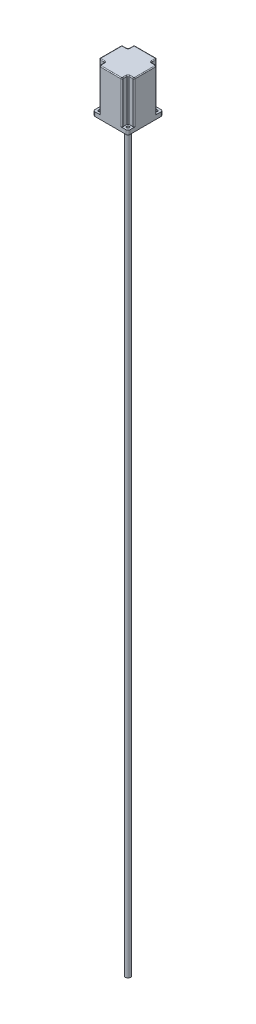
SolidWorks part; units mm, degrees
ref_plane "Спереди" through (0, 0, 0) normal (0, 0, 1) x (1, 0, 0)
ref_plane "Сверху" through (0, 0, 0) normal (0, 1, 0) x (1, 0, 0)
ref_plane "Справа" through (0, 0, 0) normal (1, 0, 0) x (0, 0, -1)
sketch "Эскиз1" plane through (0, 0, 0) normal (0, 1, 0) x (1, 0, 0)
  line L1 (-38, 43) -> (38, 43)
  line L2 (-43, 38) -> (-43, -38)
  line L3 (-38, -43) -> (38, -43)
  line L4 (43, 38) -> (43, -38)
  line L5 (-43, 43) -> (43, -43) construction
  line L6 (-43, -43) -> (43, 43) construction
  arc A1 (-38, 43) -> (-43, 38) centre (-38, 38) ccw
  arc A2 (38, 43) -> (43, 38) centre (38, 38) cw
  arc A3 (38, -43) -> (43, -38) centre (38, -38) ccw
  arc A4 (-43, -38) -> (-38, -43) centre (-38, -38) ccw
  point P0 (0, 0)
  dimension "D2" = 5
  dimension "D1" = 86
extrude "Бобышка-Вытянуть1" add sketch "Эскиз1" along normal blind 10
sketch "Эскиз2" plane through (0, 10, 0) normal (0, 1, 0) x (1, 0, 0)
  line L0 (-38, -43) -> (38, -43) construction
  line L1 (28, 43) -> (-28, 43)
  line L2 (43, 25) -> (43, -25)
  line L3 (25, -43) -> (-25, -43)
  line L4 (-43, 25) -> (-43, -25)
  line L5 (-43, 38) -> (-43, -38) construction
  line L6 (38, 43) -> (-38, 43) construction
  line L7 (43, -38) -> (43, 38) construction
  line L8 (28, -40) -> (28, -31)
  line L9 (31, -28) -> (40, -28)
  line L10 (0, 0) -> (0, 22.006) construction
  line L11 (0, 0) -> (23.6696, 0) construction
  line L12 (-31, -28) -> (-40, -28)
  line L13 (-28, -40) -> (-28, -31)
  line L14 (-28, 40) -> (-28, 31)
  line L15 (-31, 28) -> (-40, 28)
  line L16 (31, 28) -> (40, 28)
  line L17 (28, 40) -> (28, 31)
  line L18 (25, 43) -> (-25, 43)
  arc A0 (40, 28) -> (43, 25) centre (40, 25) cw
  arc A1 (31, 28) -> (28, 31) centre (31, 31) cw
  arc A2 (28, 40) -> (25, 43) centre (25, 40) ccw
  arc A3 (-28, 40) -> (-25, 43) centre (-25, 40) cw
  arc A4 (-28, 31) -> (-31, 28) centre (-31, 31) cw
  arc A5 (-40, 28) -> (-43, 25) centre (-40, 25) ccw
  arc A6 (-40, -28) -> (-43, -25) centre (-40, -25) cw
  arc A7 (-28, -40) -> (-25, -43) centre (-25, -40) ccw
  arc A8 (-31, -28) -> (-28, -31) centre (-31, -31) cw
  arc A9 (40, -28) -> (43, -25) centre (40, -25) ccw
  arc A10 (28, -40) -> (25, -43) centre (25, -40) cw
  arc A11 (28, -31) -> (31, -28) centre (31, -31) cw
  point P0 (0, 0)
  point P27 (43, 28)
  point P30 (28, 28)
  point P39 (-28, 28)
  point P42 (-43, 28)
  point P45 (-43, -28)
  point P48 (-28, -43)
  point P51 (-28, -28)
  point P54 (43, -28)
  point P57 (28, -43)
  point P60 (28, -28)
  line M12 (-43, 38) -> (-43, -38)
  line M14 (-38, -43) -> (38, -43)
  line M16 (43, -38) -> (43, 38)
  dimension "D2" = 3
  dimension "D1" = 15
extrude "Бобышка-Вытянуть2" add sketch "Эскиз2" along normal blind 104 contours L8 A11 L9 A9 A0 L16 A1 L17 A2 L1 A3 L14 A4 L15 A5 A6 L12 A8 L13 A7 A10 M16 M12 M14
sketch "Эскиз3" plane through (0, 0, 0) normal (0, -1, 0) x (1, 0, 0)
  circle A0 centre (0, 0) radius 36.5
  dimension "D1" = 73
extrude "Бобышка-Вытянуть3" add sketch "Эскиз3" along normal blind 2
sketch "Эскиз4" plane through (0, -2, 0) normal (0, -1, 0) x (1, 0, 0)
  circle A0 centre (0, 0) radius 6.35
  dimension "D1" = 12.7
extrude "Бобышка-Вытянуть4" add sketch "Эскиз4" along normal blind 35
sketch "Эскиз5" plane through (0, 114, 0) normal (0, 1, 0) x (1, 0, 0)
  circle A0 centre (0, 0) radius 6.35
  circle A1 centre (0, 0) radius 6.35 construction
sketch "Эскиз6" plane through (0, -37, 0) normal (0, -1, 0) x (1, 0, 0)
  line L0 (-3.0854, 5.55) -> (5.55, 5.55)
  line L1 (5.55, 5.55) -> (5.55, -3.0854)
  line L2 (-3.0854, 5.55) -> (-3.0854, 7.6454)
  line L3 (-3.0854, 7.6454) -> (7.5315, 7.6454)
  line L4 (7.5315, 7.6454) -> (7.5315, -3.0854)
  line L5 (7.5315, -3.0854) -> (5.55, -3.0854)
  circle A0 centre (0, 0) radius 6.35 construction
  circle A1 centre (0, 0) radius 6.35 construction
  dimension "D1" = 11.9
  dimension "D2" = 11.9
extrude "Вырез-Вытянуть1" cut sketch "Эскиз6" against normal blind 25
fillet "Скругление1" radius 2 24 edges at (-27.1213, 114, 42.1213) (-28, 114, 35.5) (-28.8787, 114, 28.8787) (-35.5, 114, 28) (-42.1213, 114, 27.1213) (-43, 114, 0) (-42.1213, 114, -27.1213) (-35.5, 114, -28) (-28.8787, 114, -28.8787) (-28, 114, -35.5) (-27.1213, 114, -42.1213) (0, 114, -43) (27.1213, 114, -42.1213) (28, 114, -35.5) (28.8787, 114, -28.8787) (35.5, 114, -28) (42.1213, 114, -27.1213) (43, 114, 0) (42.1213, 114, 27.1213) (35.5, 114, 28) (28.8787, 114, 28.8787) (28, 114, 35.5) (27.1213, 114, 42.1213) (0, 114, 43)
hole_wizard "Отверстие с зазором M61" positions "Эскиз8" profile "Эскиз9" hole size "M6" standard "GOST" end condition up to next
sketch "Эскиз8" plane through (0, 0, 0) normal (0, -1, 0) x (-1, 0, 0)
  line L0 (0, 0) -> (0, -28.1171) construction
  line L2 (0, 0) -> (29.6951, 0) construction
  point P0 (34.8, -34.8)
  point P14 (-34.8, -34.8)
  point P16 (-34.8, 34.8)
  point P17 (34.8, 34.8)
  dimension "D1" = 69.6
  dimension "D2" = 69.6
sketch "Эскиз9" plane through (-34.8, 0, 34.8) normal (1, 0, 0) x (0, 0, -1)
  line L0 (0, 0) -> (0, 10)
  line L1 (0, 10) -> (3.25, 10)
  line L2 (3.25, 10) -> (3.25, 0)
  line L5 (3.25, 0) -> (0, 0)
  line L11 (0, -6.35) -> (0, 107.95) construction
  dimension "Диаметр сквозного отверстия" = 6.5
  dimension "Глубина сквозного отверстия" = 10
sketch "Эскиз10" plane through (0, 0, -43) normal (0, 0, -1) x (-1, 0, 0)
  circle A0 centre (0, 100.9179) radius 6
  dimension "D1" = 12
extrude "Бобышка-Вытянуть6" add sketch "Эскиз10" along normal blind 2
fillet "Скругление2" radius 1.5 1 edges at (-6, 100.9179, -45)
sketch "Эскиз11" plane through (0, 0, -45) normal (0, 0, -1) x (-1, 0, 0)
  circle A0 centre (0, 100.9179) radius 2.2224
extrude "Бобышка-Вытянуть7" add sketch "Эскиз11" along normal blind 5
scale "Scale1" scale about centroid uniform scaling yes scale factor 5
sketch "Sketch1" plane through (0, -231.6505, 0) normal (0, -1, 0) x (1, 0, 0)
  circle A0 centre (0, 0) radius 32.004
  dimension "D1" = 64.008
extrude "Boss-Extrude1" add sketch "Sketch1" along normal blind 9144
